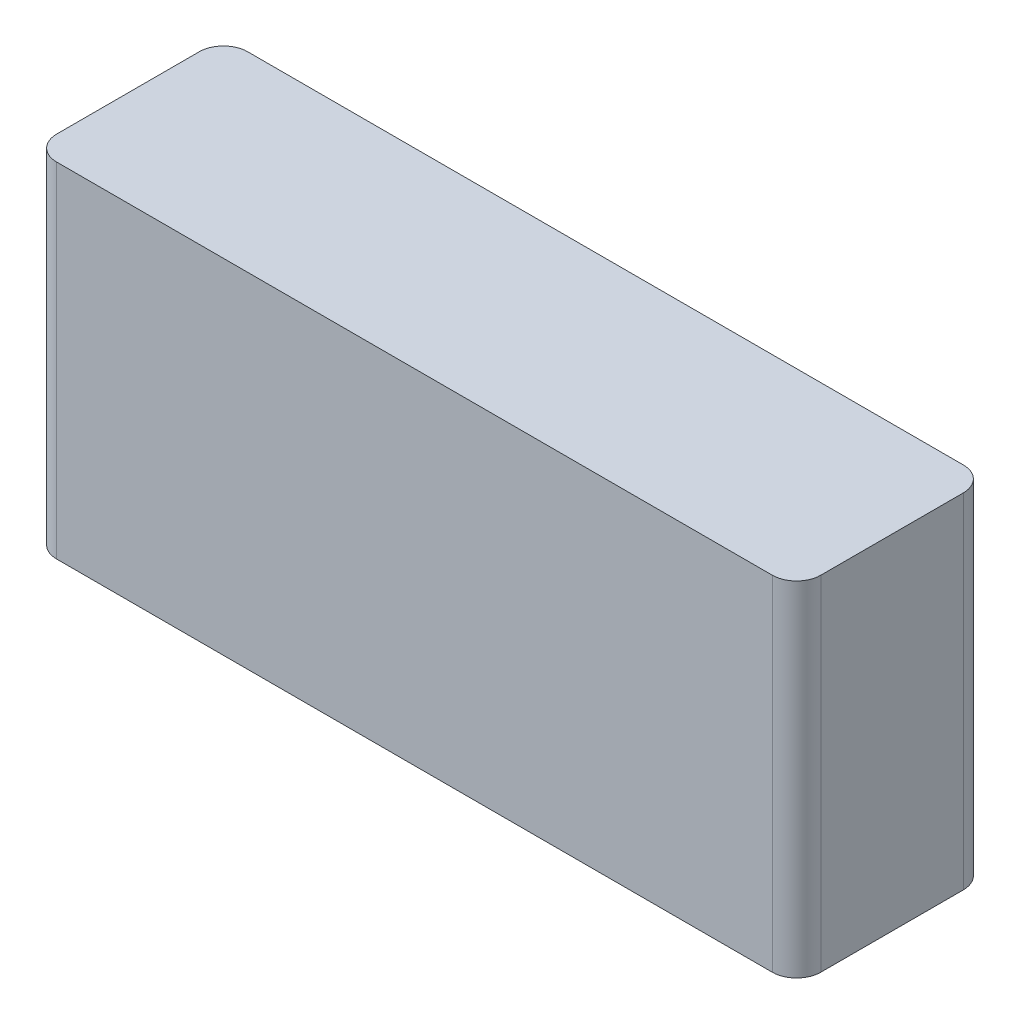
SolidWorks part; units mm, degrees
ref_plane "前视基准面" through (0, 0, 0) normal (0, 0, 1) x (1, 0, 0)
ref_plane "上视基准面" through (0, 0, 0) normal (0, 1, 0) x (1, 0, 0)
ref_plane "右视基准面" through (0, 0, 0) normal (1, 0, 0) x (0, 0, -1)
other "Configuration Table"
sketch "草图1" plane through (0, 0, 0) normal (0, 1, 0) x (1, 0, 0)
  line L1 (-37.46, 10) -> (37.46, 10)
  line L2 (-40, 7.46) -> (-40, -7.46)
  line L3 (-37.46, -10) -> (37.46, -10)
  line L4 (40, 7.46) -> (40, -7.46)
  line L5 (-40, 10) -> (40, -10) construction
  line L6 (-40, -10) -> (40, 10) construction
  arc A0 (37.46, 10) -> (40, 7.46) centre (37.46, 7.46) cw
  arc A1 (37.46, -10) -> (40, -7.46) centre (37.46, -7.46) ccw
  arc A2 (-40, -7.46) -> (-37.46, -10) centre (-37.46, -7.46) ccw
  arc A3 (-37.46, 10) -> (-40, 7.46) centre (-37.46, 7.46) ccw
  point P0 (0, 0)
  dimension "D3" = 2.54
  dimension "D1" = 80
  dimension "D2" = 20
extrude "凸台-拉伸1" add sketch "草图1" along normal blind 36
